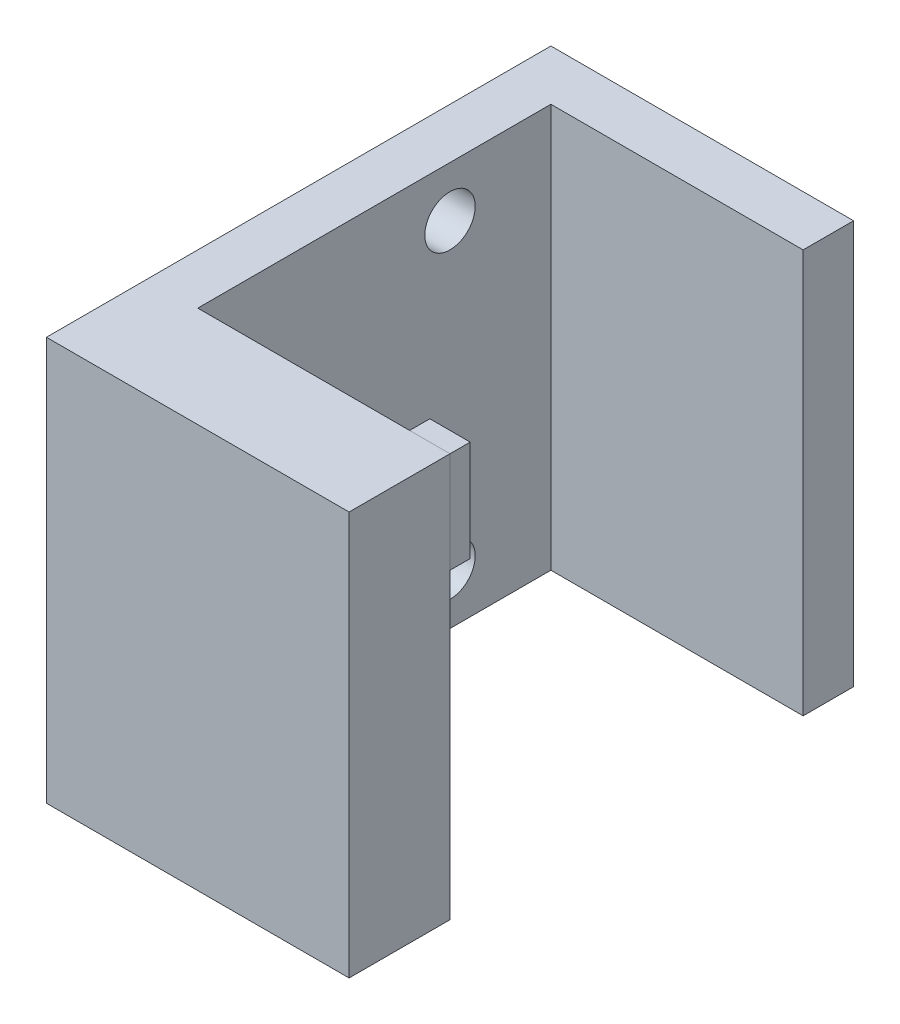
SolidWorks part; units mm, degrees
ref_plane "Front Plane" through (0, 0, 0) normal (0, 0, 1) x (1, 0, 0)
ref_plane "Top Plane" through (0, 0, 0) normal (0, 1, 0) x (1, 0, 0)
ref_plane "Right Plane" through (0, 0, 0) normal (1, 0, 0) x (0, 0, -1)
sketch "Sketch1" plane through (0, 0, 0) normal (0, 1, 0) x (1, 0, 0)
  line L0 (0, 225) -> (0, 250)
  line L1 (0, 0) -> (-150, 0)
  line L2 (0, 0) -> (0, 50)
  line L3 (0, 250) -> (-150, 250)
  line L4 (-150, 0) -> (-150, 250)
  line L5 (0, 50) -> (-125, 50)
  line L7 (0, 225) -> (-125, 225)
  line L8 (-125, 50) -> (-125, 225)
  dimension "D1" = 25
  dimension "D2" = 50
  dimension "D3" = 25
  dimension "D4" = 250
  dimension "D5" = 150
extrude "Boss-Extrude1" add sketch "Sketch1" along normal blind 200
sketch "Sketch2" plane through (-150, 0, 0) normal (-1, 0, 0) x (0, 0, 1)
  line L0 (-175, 175) -> (-175, 25) construction
  line L1 (-250, 200) -> (-250, 0) construction
  point P4 (-250, 100)
  point P5 (-175, 100)
  dimension "D1" = 75
  dimension "D2" = 150
hole_wizard "Hole1" positions "3DSketch1" profile "Sketch3" legacy end condition through all
sketch3d "3DSketch1"
  point P0 (-150, 175, -175)
  point P3 (-150, 25, -175)
sketch "Sketch3" plane through (-150, 175, -175) normal (0, 1, 0) x (0, 0, 1)
  line L0 (0, 0) -> (0, 150)
  line L1 (0, 150) -> (12.5, 150)
  line L2 (12.5, 150) -> (12.5, 0)
  line L3 (12.5, 0) -> (0, 0)
  line L4 (0, 110) -> (0, -10) construction
  dimension "Diameter" = 25
  dimension "Depth" = 150
sketch "Sketch4" plane through (0, 0, -50) normal (0, 0, -1) x (-1, 0, 0)
  line L1 (0, 200) -> (20, 200)
  line L2 (0, 200) -> (0, 150)
  line L3 (0, 150) -> (20, 150)
  line L4 (20, 200) -> (20, 150)
  dimension "D1" = 20
  dimension "D2" = 50
extrude "Boss-Extrude2" add sketch "Sketch4" along normal blind 10 separate body
